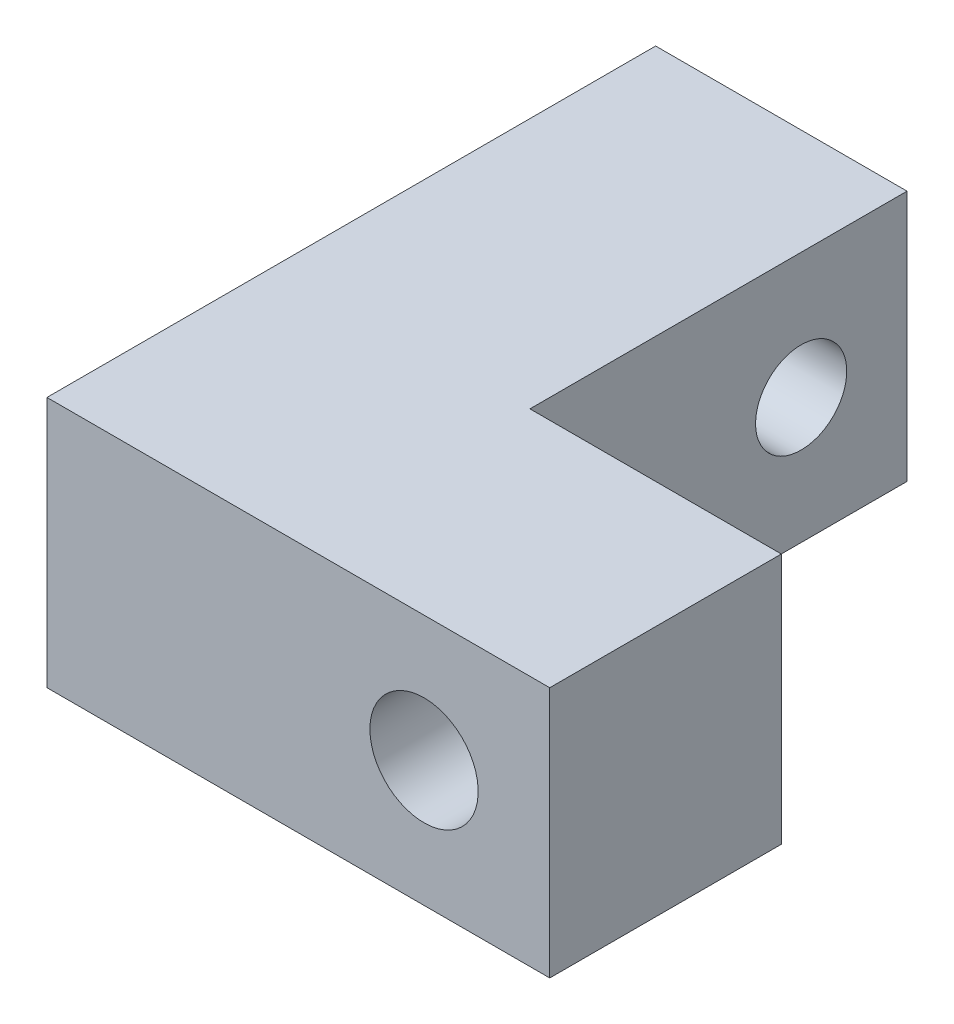
SolidWorks part; units mm, degrees
ref_plane "Front Plane" through (0, 0, 0) normal (0, 0, 1) x (1, 0, 0)
ref_plane "Top Plane" through (0, 0, 0) normal (0, 1, 0) x (1, 0, 0)
ref_plane "Right Plane" through (0, 0, 0) normal (1, 0, 0) x (0, 0, -1)
sketch "Sketch1" plane through (0, 0, 0) normal (0, 1, 0) x (1, 0, 0)
  line L1 (-19.05, -23.8125) -> (19.05, -23.8125)
  line L2 (-19.05, -23.8125) -> (-19.05, 23.8125)
  line L3 (-19.05, 23.8125) -> (19.05, 23.8125)
  line L4 (19.05, -23.8125) -> (19.05, 23.8125)
  line L5 (-19.05, -23.8125) -> (19.05, 23.8125) construction
  line L6 (-19.05, 23.8125) -> (19.05, -23.8125) construction
  point P0 (0, 0)
  dimension "D1" = 38.1
  dimension "D2" = 47.625
extrude "Boss-Extrude1" add sketch "Sketch1" along normal blind 19.05
sketch "Sketch2" plane through (0, 19.05, 0) normal (0, 1, 0) x (1, 0, 0)
  line L0 (-19.05, 23.8125) -> (-19.05, -23.8125) construction
  line L1 (19.05, 23.8125) -> (0, 23.8125)
  line L2 (19.05, 23.8125) -> (19.05, -4.7625)
  line L3 (19.05, -4.7625) -> (0, -4.7625)
  line L4 (0, 23.8125) -> (0, -4.7625)
  line L5 (-19.05, -23.8125) -> (19.05, -23.8125) construction
  dimension "D1" = 19.05
  dimension "D2" = 19.05
extrude "Cut-Extrude1" cut sketch "Sketch2" against normal up to next
hole_wizard "5/16-24 Tapped Hole1" positions "Sketch4" profile "Sketch3" tap size "5/16-24" standard "Ansi Inch"
sketch "Sketch4" plane through (-19.05, 0, 0) normal (-1, 0, 0) x (0, 0, 1)
  line L1 (-23.8125, 9.525) -> (-14.2875, 9.525) construction
  line L2 (-23.8125, 19.05) -> (-23.8125, 0) construction
  line L3 (11.1125, 9.525) -> (-14.2875, 9.525) construction
  line L4 (23.8125, 19.05) -> (23.8125, 0) construction
  point P0 (-14.2875, 9.525)
  point P1 (11.1125, 9.525)
  dimension "D1" = 12.7
  dimension "D2" = 25.4
sketch "Sketch3" plane through (-19.05, 9.525, -14.2875) normal (0, 1, 0) x (0, 0, 1)
  line L0 (0, 0) -> (0, 21.1356)
  line L1 (0, 21.1356) -> (3.4544, 19.06)
  line L2 (3.4544, 19.06) -> (3.4544, 1.1494)
  line L3 (3.4544, 1.1494) -> (4.6037, 0)
  line L5 (4.6037, 0) -> (0, 0)
  line L6 (-3.4544, 1.1494) -> (-4.6037, 0) construction
  line L10 (0, 21.1356) -> (-3.4544, 19.06) construction
  line L11 (0, -6.35) -> (0, 107.95) construction
  dimension "Tap Drill Dia." = 6.9088
  dimension "Tap Drill Depth" = 19.06
  dimension "Near C'Sink Dia." = 9.2075
  dimension "Near C'Sink Angle" = 90
  dimension "Drill Angle" = 118
cosmetic thread "Hole Thread1" parameters "D1"=15.88, "D2"=7.9375
cosmetic thread "Hole Thread2" parameters "D1"=15.88, "D2"=7.9375
hole_wizard "5/16 Clearance Hole1" positions "Sketch6" profile "Sketch5" hole size "5/16" standard "Ansi Inch" end condition through all
sketch "Sketch6" plane through (0, 0, 4.7625) normal (0, 0, -1) x (-1, 0, 0)
  line L1 (-19.05, 9.525) -> (-9.525, 9.525) construction
  line L2 (-19.05, 0) -> (-19.05, 19.05) construction
  point P1 (-9.525, 9.525)
  dimension "D1" = 9.525
sketch "Sketch5" plane through (9.525, 9.525, 4.7625) normal (1, 0, 0) x (0, 1, 0)
  line L0 (0, 0) -> (0, 19.05)
  line L1 (0, 19.05) -> (4.1021, 19.05)
  line L2 (4.1021, 19.05) -> (4.1021, 0.635)
  line L3 (4.1021, 0.635) -> (4.7371, 0)
  line L5 (4.7371, 0) -> (0, 0)
  line L6 (-4.1021, 0.635) -> (-4.7371, 0) construction
  line L11 (0, -6.35) -> (0, 107.95) construction
  dimension "Thru Hole Dia." = 8.2042
  dimension "Thru Hole Depth" = 19.05
  dimension "Near C'Sink Dia." = 9.4742
  dimension "Near C'Sink Angle" = 90
chamfer "Chamfer1" distance 1.5 angle 45 6 edges at (9.525, 0, 4.7625) (9.525, 19.05, 4.7625) (19.05, 9.525, 4.7625) (-9.525, 0, -23.8125) (-9.525, 19.05, -23.8125) (0, 9.525, -23.8125)
